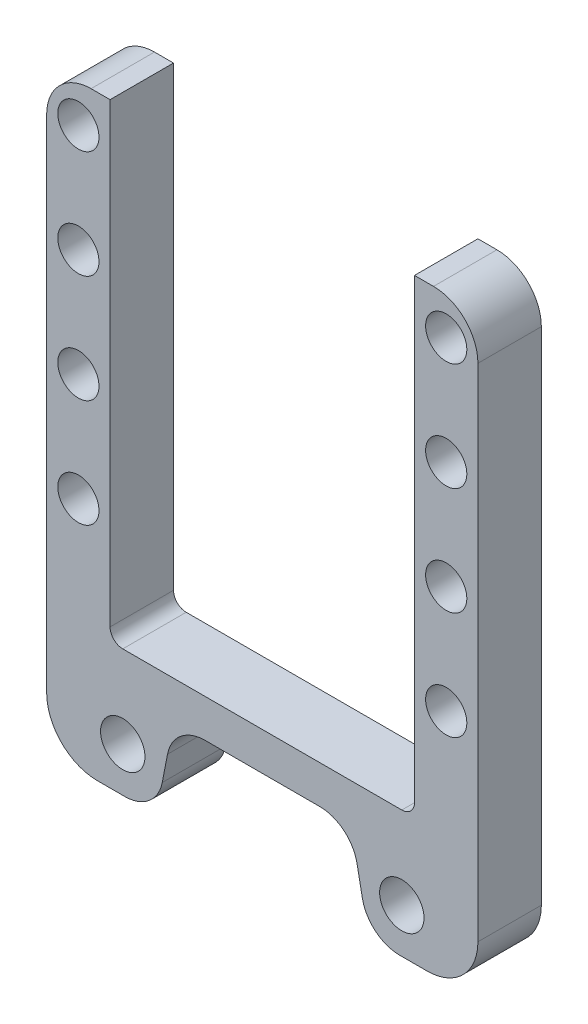
SolidWorks part; units mm, degrees
ref_plane "Plan de face" through (0, 0, 0) normal (0, 0, 1) x (1, 0, 0)
ref_plane "Plan de dessus" through (0, 0, 0) normal (0, 1, 0) x (1, 0, 0)
ref_plane "Plan de droite" through (0, 0, 0) normal (1, 0, 0) x (0, 0, -1)
sketch "Esquisse1" plane through (0, 0, 0) normal (0, 0, 1) x (1, 0, 0)
  line L0 (24, 110) -> (24, 36)
  line L1 (24, 36) -> (0, 36)
  line L7 (0, 30) -> (14, 30)
  line L8 (14, 30) -> (16.7213, 16)
  line L9 (16.7213, 16) -> (34, 16)
  line L10 (34, 16) -> (34, 110)
  line L11 (34, 110) -> (24, 110)
  line L12 (0, 36) -> (0, 30)
  line L13 (0, -0.15) -> (0, 72.4519) construction
  circle A0 centre (29, 104) radius 3.25
  circle A1 centre (22, 23) radius 3.5
  circle A2 centre (29, 87) radius 3.25
  circle A3 centre (29, 70) radius 3.25
  circle A4 centre (29, 53) radius 3.25
  point P19 (29, 110)
  point P22 (29, 80.1623)
  point P23 (30.1727, 87.1877)
  point P24 (0, 0)
  dimension "D9" = 7
  dimension "D10" = 6
  dimension "D14" = 6.5
  dimension "D1" = 6
  dimension "D2" = 24
  dimension "D3" = 101
  dimension "D4" = 30
  dimension "D5" = 10
  dimension "D6" = 74
  dimension "D7" = 14
  dimension "D8" = 14
  dimension "D11" = 34
  dimension "D12" = 7
  dimension "D13" = 22
  dimension "D15" = 34
  dimension "D16" = 17
extrude "Boss.-Extru.1" add sketch "Esquisse1" along normal blind 10
mirror "Symétrie2" about plane through (0, 36, 10) normal (1, 0, 0) of "Boss.-Extru.1"
fillet "Congé1" radius 6 4 edges at (16.7213, 16, 5) (-16.7213, 16, 5) (-14, 30, 5) (14, 30, 5)
fillet "Congé2" radius 8 2 edges at (-34, 16, 5) (34, 16, 5)
fillet "Congé3" radius 7 2 edges at (34, 110, 5) (-34, 110, 5)
fillet "Congé4" radius 2 2 edges at (-24, 36, 5) (24, 36, 5)
